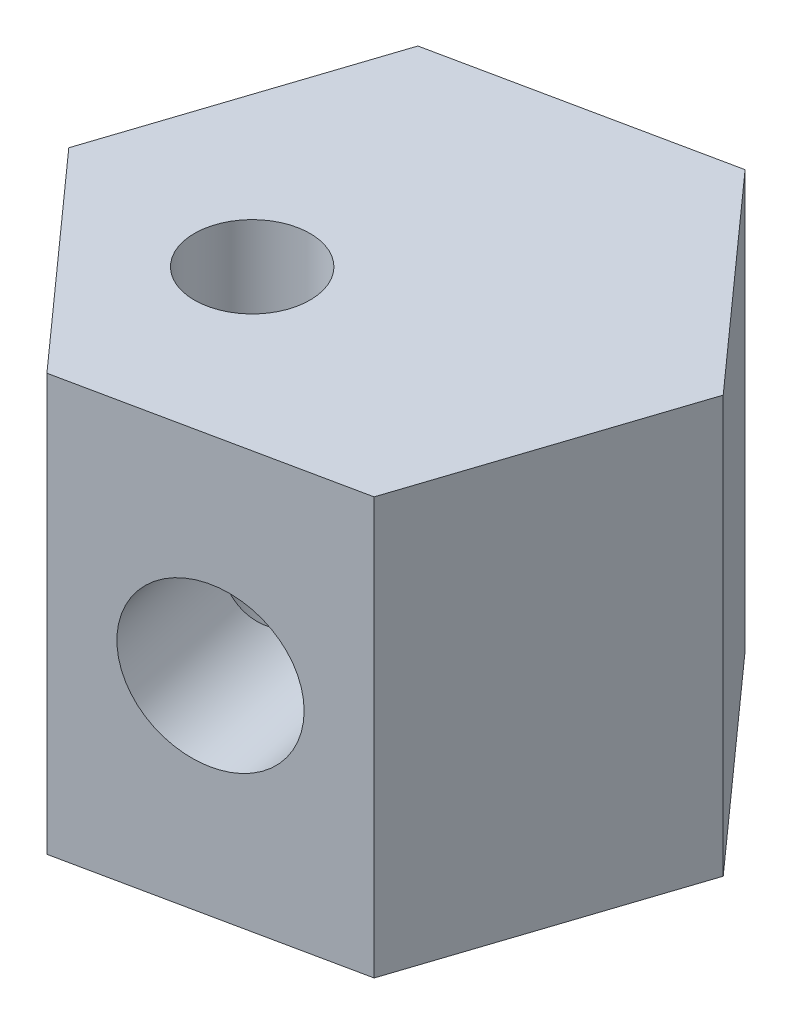
SolidWorks part; units mm, degrees
ref_plane "Front Plane" through (0, 0, 0) normal (0, 0, 1) x (1, 0, 0)
ref_plane "Top Plane" through (0, 0, 0) normal (0, 1, 0) x (1, 0, 0)
ref_plane "Right Plane" through (0, 0, 0) normal (1, 0, 0) x (0, 0, -1)
sketch "Sketch1" plane through (0, 0, 0) normal (0, 1, 0) x (1, 0, 0)
  line L1 (5.9788, 18.1757) -> (-12.7512, 14.2657)
  line L2 (-12.7512, 14.2657) -> (-18.73, -3.91)
  line L3 (-18.73, -3.91) -> (-5.9788, -18.1757)
  line L4 (-5.9788, -18.1757) -> (12.7512, -14.2657)
  line L5 (12.7512, -14.2657) -> (18.73, 3.91)
  line L6 (18.73, 3.91) -> (5.9788, 18.1757)
  circle A0 centre (0, 0) radius 16.5703 construction
  dimension "D1" = 18.73
extrude "Boss-Extrude1" add sketch "Sketch1" along normal blind 28.83
sketch "Sketch2" plane through (3.3862, 0, 16.2207) normal (0.2044, 0, 0.9789) x (0.9789, 0, -0.2044)
  line L0 (0, 28.83) -> (0, 0) construction
  line L1 (-9.5669, 28.83) -> (9.5669, 28.83) construction
  line L2 (-9.5669, 14.415) -> (9.5669, 14.415) construction
  line L3 (-9.5669, 28.83) -> (-9.5669, 0) construction
  line L4 (9.5669, 28.83) -> (9.5669, 0) construction
  circle A0 centre (0, 14.415) radius 5.475
  dimension "D1" = 10.95
extrude "Cut-Extrude1" cut sketch "Sketch2" against normal blind 82
sketch "Sketch3" plane through (0, 28.83, 0) normal (0, 1, 0) x (1, 0, 0)
  line L0 (-12.7512, 14.2657) -> (-5.9788, -18.1757) construction
  line L1 (-18.73, -3.91) -> (12.7512, -14.2657) construction
  line L2 (-8.2363, -7.3619) -> (12.3544, 11.0428) construction
  line L3 (18.73, 3.91) -> (5.9788, 18.1757) construction
  line L4 (-3.3862, 16.2207) -> (3.3862, -16.2207) construction
  line L5 (5.9788, 18.1757) -> (-12.7512, 14.2657) construction
  line L6 (-5.9788, -18.1757) -> (12.7512, -14.2657) construction
  circle A0 centre (-5.254, -4.6962) radius 4
  dimension "D1" = 8
extrude "Cut-Extrude4" cut sketch "Sketch3" against normal through all contours A0
